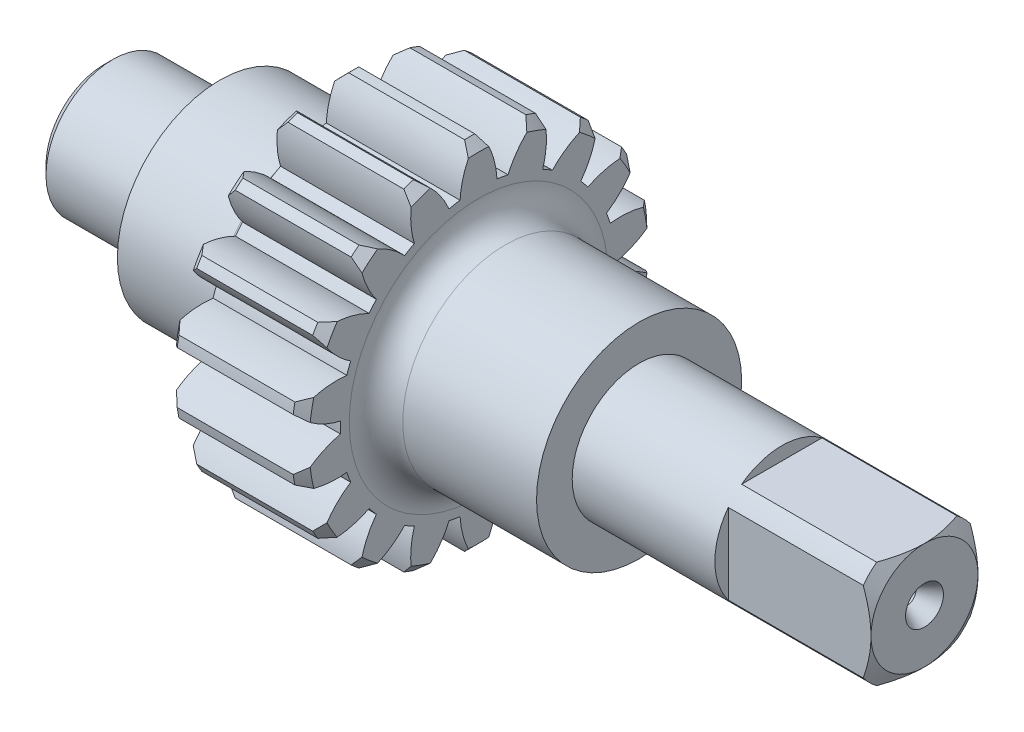
SolidWorks part; units mm, degrees
ref_plane "Front Plane" through (0, 0, 0) normal (0, 0, 1) x (1, 0, 0)
ref_plane "Top Plane" through (0, 0, 0) normal (0, 1, 0) x (1, 0, 0)
ref_plane "Right Plane" through (0, 0, 0) normal (1, 0, 0) x (0, 0, -1)
sketch "Sketch2" plane through (0, 0, 0) normal (0, 0, 1) x (1, 0, 0)
  line L0 (0, 0) -> (92, 0)
  line L1 (92, 0) -> (92, 7.5)
  line L2 (92, 7.5) -> (60, 7.5)
  line L3 (60, 7.5) -> (60, 11.5)
  line L4 (60, 11.5) -> (45, 11.5)
  line L5 (42, 14.5) -> (42, 15.5)
  line L6 (42, 15.5) -> (27, 15.5)
  line L7 (27, 15.5) -> (27, 14.5)
  line L8 (24, 11.5) -> (13, 11.5)
  line L9 (13, 11.5) -> (13, 7.5)
  line L10 (13, 7.5) -> (0, 7.5)
  line L11 (0, 7.5) -> (0, 0)
  arc A0 (45, 11.5) -> (42, 14.5) centre (45, 14.5) cw
  arc A1 (27, 14.5) -> (24, 11.5) centre (24, 14.5) cw
  point P17 (27, 11.5)
  dimension "D9" = 3
  dimension "D1" = 13
  dimension "D2" = 14
  dimension "D3" = 47
  dimension "D4" = 15
  dimension "D5" = 92
  dimension "D6" = 7.5
  dimension "D7" = 11.5
  dimension "D8" = 15.5
revolve "Revolve1" add sketch "Sketch2" angle 360 about L0
sketch "Sketch3" plane through (42, 0, 0) normal (1, 0, 0) x (0, 0, -1)
  line L0 (0, 15.5) -> (0, 0) construction
  circle A0 centre (0, 0) radius 15.5 construction
  arc A1 (0.57, 19.9919) -> (-0.57, 19.9919) centre (0, 0) ccw
  circle A2 centre (0, 0) radius 18 construction
  arc A3 (2.07, 15.3612) -> (-2.07, 15.3612) centre (0, 0) ccw
  arc A4 (7.199, 13.7268) -> (3.3087, 15.1427) centre (0, 0) ccw
  arc A5 (7.3732, 18.5913) -> (6.302, 18.9812) centre (0, 0) ccw
  arc A6 (11.4597, 10.4368) -> (8.2882, 13.0979) centre (0, 0) ccw
  arc A7 (13.2872, 14.9483) -> (12.4139, 15.6811) centre (0, 0) ccw
  arc A8 (14.3382, 5.8879) -> (12.2682, 9.4733) centre (0, 0) ccw
  arc A9 (17.5985, 9.5023) -> (17.0285, 10.4896) centre (0, 0) ccw
  arc A10 (15.4872, 0.6289) -> (14.7683, 4.706) centre (0, 0) ccw
  arc A11 (19.7871, 2.9102) -> (19.5892, 4.0329) centre (0, 0) ccw
  arc A12 (14.7683, -4.706) -> (15.4872, -0.6289) centre (0, 0) ccw
  arc A13 (19.5892, -4.0329) -> (19.7871, -2.9102) centre (0, 0) ccw
  arc A14 (12.2682, -9.4733) -> (14.3382, -5.8879) centre (0, 0) ccw
  arc A15 (17.0285, -10.4896) -> (17.5985, -9.5023) centre (0, 0) ccw
  arc A16 (8.2882, -13.0979) -> (11.4597, -10.4368) centre (0, 0) ccw
  arc A17 (12.4139, -15.6811) -> (13.2872, -14.9483) centre (0, 0) ccw
  arc A18 (3.3087, -15.1427) -> (7.199, -13.7268) centre (0, 0) ccw
  arc A19 (6.302, -18.9812) -> (7.3732, -18.5913) centre (0, 0) ccw
  arc A20 (-2.07, -15.3612) -> (2.07, -15.3612) centre (0, 0) ccw
  arc A21 (-0.57, -19.9919) -> (0.57, -19.9919) centre (0, 0) ccw
  arc A22 (-7.199, -13.7268) -> (-3.3087, -15.1427) centre (0, 0) ccw
  arc A23 (-7.3732, -18.5913) -> (-6.302, -18.9812) centre (0, 0) ccw
  arc A24 (-11.4597, -10.4368) -> (-8.2882, -13.0979) centre (0, 0) ccw
  arc A25 (-13.2872, -14.9483) -> (-12.4139, -15.6811) centre (0, 0) ccw
  arc A26 (-14.3382, -5.8879) -> (-12.2682, -9.4733) centre (0, 0) ccw
  arc A27 (-17.5985, -9.5023) -> (-17.0285, -10.4896) centre (0, 0) ccw
  arc A28 (-15.4872, -0.6289) -> (-14.7683, -4.706) centre (0, 0) ccw
  arc A29 (-19.7871, -2.9102) -> (-19.5892, -4.0329) centre (0, 0) ccw
  arc A30 (-14.7683, 4.706) -> (-15.4872, 0.6289) centre (0, 0) ccw
  arc A31 (-19.5892, 4.0329) -> (-19.7871, 2.9102) centre (0, 0) ccw
  arc A32 (-12.2682, 9.4733) -> (-14.3382, 5.8879) centre (0, 0) ccw
  arc A33 (-17.0285, 10.4896) -> (-17.5985, 9.5023) centre (0, 0) ccw
  arc A34 (-8.2882, 13.0979) -> (-11.4597, 10.4368) centre (0, 0) ccw
  arc A35 (-12.4139, 15.6811) -> (-13.2872, 14.9483) centre (0, 0) ccw
  arc A36 (-3.3087, 15.1427) -> (-7.199, 13.7268) centre (0, 0) ccw
  arc A37 (-6.302, 18.9812) -> (-7.3732, 18.5913) centre (0, 0) ccw
  spline S0 degree 2 poles (-0.57, 19.9919) (-1.923, 17.8777) (-2.07, 15.3612) knots 0 0 0 1 1 1
  spline S1 degree 2 poles (0.57, 19.9919) (1.923, 17.8777) (2.07, 15.3612) knots 0 0 0 1 1 1
  spline S2 degree 2 poles (6.302, 18.9812) (4.3075, 17.4572) (3.3087, 15.1427) knots 0 0 0 1 1 1
  spline S3 degree 2 poles (7.3732, 18.5913) (7.9215, 16.1418) (7.199, 13.7268) knots 0 0 0 1 1 1
  spline S4 degree 2 poles (12.4139, 15.6811) (10.0185, 14.9311) (8.2882, 13.0979) knots 0 0 0 1 1 1
  spline S5 degree 2 poles (13.2872, 14.9483) (12.9646, 12.459) (11.4597, 10.4368) knots 0 0 0 1 1 1
  spline S6 degree 2 poles (17.0285, 10.4896) (14.521, 10.6042) (12.2682, 9.4733) knots 0 0 0 1 1 1
  spline S7 degree 2 poles (17.5985, 9.5023) (16.444, 7.2735) (14.3382, 5.8879) knots 0 0 0 1 1 1
  spline S8 degree 2 poles (19.5892, 4.0329) (17.2721, 4.9982) (14.7683, 4.706) knots 0 0 0 1 1 1
  spline S9 degree 2 poles (19.7871, 2.9102) (17.94, 1.2107) (15.4872, 0.6289) knots 0 0 0 1 1 1
  spline S10 degree 2 poles (19.7871, -2.9102) (17.94, -1.2107) (15.4872, -0.6289) knots 0 0 0 1 1 1
  spline S11 degree 2 poles (19.5892, -4.0329) (17.2721, -4.9982) (14.7683, -4.706) knots 0 0 0 1 1 1
  spline S12 degree 2 poles (17.5985, -9.5023) (16.444, -7.2735) (14.3382, -5.8879) knots 0 0 0 1 1 1
  spline S13 degree 2 poles (17.0285, -10.4896) (14.521, -10.6042) (12.2682, -9.4733) knots 0 0 0 1 1 1
  spline S14 degree 2 poles (13.2872, -14.9483) (12.9646, -12.459) (11.4597, -10.4368) knots 0 0 0 1 1 1
  spline S15 degree 2 poles (12.4139, -15.6811) (10.0185, -14.9311) (8.2882, -13.0979) knots 0 0 0 1 1 1
  spline S16 degree 2 poles (7.3732, -18.5913) (7.9215, -16.1418) (7.199, -13.7268) knots 0 0 0 1 1 1
  spline S17 degree 2 poles (6.302, -18.9812) (4.3075, -17.4572) (3.3087, -15.1427) knots 0 0 0 1 1 1
  spline S18 degree 2 poles (0.57, -19.9919) (1.923, -17.8777) (2.07, -15.3612) knots 0 0 0 1 1 1
  spline S19 degree 2 poles (-0.57, -19.9919) (-1.923, -17.8777) (-2.07, -15.3612) knots 0 0 0 1 1 1
  spline S20 degree 2 poles (-6.302, -18.9812) (-4.3075, -17.4572) (-3.3087, -15.1427) knots 0 0 0 1 1 1
  spline S21 degree 2 poles (-7.3732, -18.5913) (-7.9215, -16.1418) (-7.199, -13.7268) knots 0 0 0 1 1 1
  spline S22 degree 2 poles (-12.4139, -15.6811) (-10.0185, -14.9311) (-8.2882, -13.0979) knots 0 0 0 1 1 1
  spline S23 degree 2 poles (-13.2872, -14.9483) (-12.9646, -12.459) (-11.4597, -10.4368) knots 0 0 0 1 1 1
  spline S24 degree 2 poles (-17.0285, -10.4896) (-14.521, -10.6042) (-12.2682, -9.4733) knots 0 0 0 1 1 1
  spline S25 degree 2 poles (-17.5985, -9.5023) (-16.444, -7.2735) (-14.3382, -5.8879) knots 0 0 0 1 1 1
  spline S26 degree 2 poles (-19.5892, -4.0329) (-17.2721, -4.9982) (-14.7683, -4.706) knots 0 0 0 1 1 1
  spline S27 degree 2 poles (-19.7871, -2.9102) (-17.94, -1.2107) (-15.4872, -0.6289) knots 0 0 0 1 1 1
  spline S28 degree 2 poles (-19.7871, 2.9102) (-17.94, 1.2107) (-15.4872, 0.6289) knots 0 0 0 1 1 1
  spline S29 degree 2 poles (-19.5892, 4.0329) (-17.2721, 4.9982) (-14.7683, 4.706) knots 0 0 0 1 1 1
  spline S30 degree 2 poles (-17.5985, 9.5023) (-16.444, 7.2735) (-14.3382, 5.8879) knots 0 0 0 1 1 1
  spline S31 degree 2 poles (-17.0285, 10.4896) (-14.521, 10.6042) (-12.2682, 9.4733) knots 0 0 0 1 1 1
  spline S32 degree 2 poles (-13.2872, 14.9483) (-12.9646, 12.459) (-11.4597, 10.4368) knots 0 0 0 1 1 1
  spline S33 degree 2 poles (-12.4139, 15.6811) (-10.0185, 14.9311) (-8.2882, 13.0979) knots 0 0 0 1 1 1
  spline S34 degree 2 poles (-7.3732, 18.5913) (-7.9215, 16.1418) (-7.199, 13.7268) knots 0 0 0 1 1 1
  spline S35 degree 2 poles (-6.302, 18.9812) (-4.3075, 17.4572) (-3.3087, 15.1427) knots 0 0 0 1 1 1
  point P117 (0, 0)
  dimension "D1" = 40
  dimension "D2" = 36
  dimension "D3" = 0.5
  dimension "D4" = 2.07
  dimension "D5" = 0.57
  dimension "D6" = 18
extrude "Boss-Extrude1" add sketch "Sketch3" against normal up to surface (15 mm away) up to face at (27, 0, 14.5)
sketch "Sketch4" plane through (0, 0, 0) normal (0, 1, 0) x (1, 0, 0)
  line L0 (92, 0) -> (72.0944, 0) construction
  line L1 (92, -7.5) -> (92, 7.5) construction
  line L2 (86.75, 0) -> (92, 0)
  line L3 (92, 0) -> (92, 2.1258)
  line L4 (92, 2.1258) -> (90.05, 1)
  line L5 (90.05, 1) -> (88.25, 1)
  line L6 (88.25, 1) -> (86.75, 0)
  line L7 (46, 28.1172) -> (46, -32.4349) construction
  line L8 (0, 7.5) -> (0, -7.5) construction
  line L9 (5.25, 0) -> (0, 0)
  line L10 (0, 0) -> (0, 2.1258)
  line L11 (0, 2.1258) -> (1.95, 1)
  line L12 (1.95, 1) -> (3.75, 1)
  line L13 (3.75, 1) -> (5.25, 0)
  dimension "D1" = 30
  dimension "D2" = 1
  dimension "D3" = 3.3
  dimension "D4" = 1.8
  dimension "D5" = 1.95
  dimension "D6" = 46
revolve "Cut-Revolve1" cut sketch "Sketch4" angle 360 about L0
chamfer "Chamfer1" distance 1 angle 45 1 edges at (0, 0, 7.5)
chamfer "Chamfer2" distance 1.5 angle 30 1 edges at (92, 0, 7.5)
sketch "Sketch7" plane through (92, 0, 0) normal (1, 0, 0) x (0, 0, -1)
  line L0 (-6, 6) -> (0, 11)
  line L1 (-6, 6) -> (6, 6)
  line L2 (-6, 6) -> (-6, -6)
  line L3 (-6, -6) -> (6, -6)
  line L4 (6, 6) -> (6, -6)
  line L5 (-6, 6) -> (6, -6) construction
  line L6 (-6, -6) -> (6, 6) construction
  line L7 (0, 11) -> (6, 6)
  line L8 (11, 0) -> (6, -6)
  line L9 (6, 6) -> (11, 0)
  line L10 (0, -11) -> (-6, -6)
  line L11 (6, -6) -> (0, -11)
  line L12 (-11, 0) -> (-6, 6)
  line L13 (-6, -6) -> (-11, 0)
  circle A0 centre (0, 0) radius 6 construction
  circle A1 centre (0, 0) radius 6
  point P20 (0, 0)
  dimension "D1" = 5
  dimension "D2" = 4
extrude "Cut-Extrude2" cut sketch "Sketch7" against normal blind 16 contours L7 L0 L1 | L9 L4 L8 | L13 L2 L12 | L11 L3 L10
chamfer "Chamfer3" distance 1 angle 45 18 edges at (42, -18.7939, -6.8404) (42, -15.3209, -12.8558) (42, -10, -17.3205) (42, -3.473, -19.6962) (42, 3.473, -19.6962) (42, 10, -17.3205) (42, 15.3209, -12.8558) (42, 18.7939, -6.8404) (42, 20, 0) (42, 18.7939, 6.8404) (42, 15.3209, 12.8558) (42, 10, 17.3205) (42, 3.473, 19.6962) (42, -3.473, 19.6962) (42, -10, 17.3205) (42, -20, 0) (42, -18.7939, 6.8404) (42, -15.3209, 12.8558)
chamfer "Chamfer4" distance 1 angle 45 18 edges at (27, -18.7939, -6.8404) (27, -20, 0) (27, -18.7939, 6.8404) (27, -15.3209, 12.8558) (27, -10, 17.3205) (27, -3.473, 19.6962) (27, 3.473, 19.6962) (27, 10, 17.3205) (27, 15.3209, 12.8558) (27, 18.7939, 6.8404) (27, 20, 0) (27, 18.7939, -6.8404) (27, 15.3209, -12.8558) (27, 10, -17.3205) (27, 3.473, -19.6962) (27, -15.3209, -12.8558) (27, -3.473, -19.6962) (27, -10, -17.3205)
